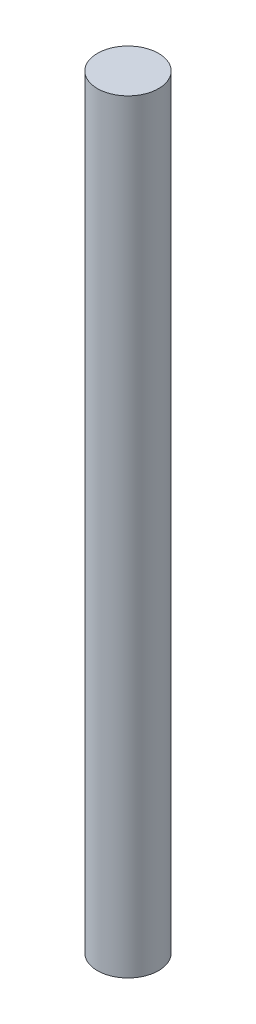
SolidWorks part; units mm, degrees
ref_plane "Front" through (0, 0, 0) normal (0, 0, 1) x (1, 0, 0)
ref_plane "Top" through (0, 0, 0) normal (0, 1, 0) x (1, 0, 0)
ref_plane "Right" through (0, 0, 0) normal (1, 0, 0) x (0, 0, -1)
sketch "Sketch1" plane through (0, 0, 0) normal (0, 1, 0) x (1, 0, 0)
  circle A0 centre (0, 0) radius 5
  dimension "D1" = 10
extrude "Boss-Extrude1" add sketch "Sketch1" along normal blind 125
sketch "Sketch2" plane through (0, 0, 0) normal (0, 0, 1) x (1, 0, 0)
  line L0 (0, 0) -> (0, 125) construction
  line L1 (5, 125) -> (-5, 125) construction
  point P6 (0, 62.5)
